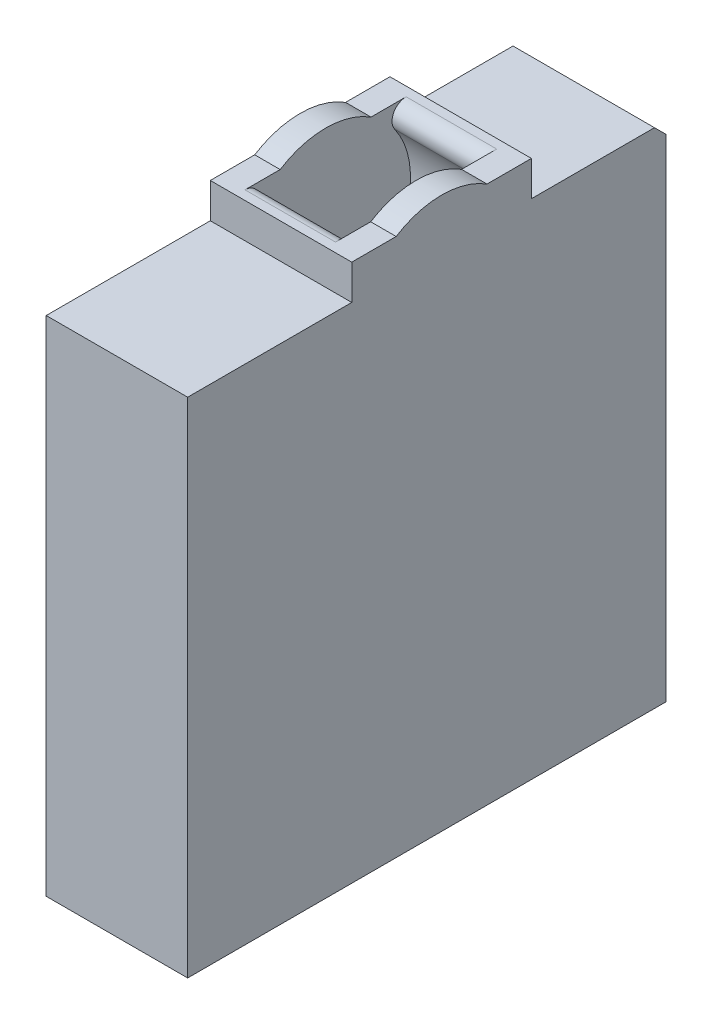
SolidWorks part; units mm, degrees
material "ABS"
ref_plane "Front Plane" through (0, 0, 0) normal (0, 0, 1) x (1, 0, 0)
ref_plane "Top Plane" through (0, 0, 0) normal (0, 1, 0) x (1, 0, 0)
ref_plane "Right Plane" through (0, 0, 0) normal (1, 0, 0) x (0, 0, -1)
sketch "Sketch1" plane through (0, 0, 0) normal (1, 0, 0) x (0, 0, -1)
  line L0 (-44.875, -95.07) -> (-44.875, -6.17)
  line L1 (-44.875, -6.17) -> (-15.875, -6.17)
  line L2 (-15.875, -6.17) -> (-15.875, 0)
  line L3 (-15.875, 0) -> (15.875, 0)
  line L4 (15.875, 0) -> (15.875, -6.17)
  line L5 (15.875, -6.17) -> (39.625, -6.17)
  line L6 (39.625, -6.17) -> (39.625, -95.07)
  line L7 (39.625, -95.07) -> (-44.875, -95.07)
  point P4 (0, 0)
  dimension "D1" = 88.9
  dimension "D2" = 6.17
  dimension "D3" = 29
  dimension "D4" = 23.75
  dimension "D5" = 31.75
extrude "Boss-Extrude1" add sketch "Sketch1" along normal blind 25
sketch "Sketch2" plane through (25, 0, 0) normal (1, 0, 0) x (0, 0, -1)
  line L0 (-15.875, -6.17) -> (15.875, -6.17) construction
  line L1 (0, -6.17) -> (0, 2.33) construction
  line L2 (-8.0294, 0) -> (8.0294, 0)
  line L3 (15.875, 0) -> (-15.875, 0) construction
  arc A0 (8.0294, 0) -> (-8.0294, 0) centre (0, -12.67) ccw
  dimension "D2" = 30
  dimension "D1" = 8.5
extrude "Boss-Extrude2" add sketch "Sketch2" against normal up to surface (25 mm away) up to face at (0, -26.8525, 1.3125)
sketch "Sketch3" plane through (25, 0, 0) normal (1, 0, 0) x (0, 0, -1)
  circle A0 centre (0, -12.67) radius 15
  arc A1 (8.0294, 0) -> (-8.0294, 0) centre (0, -12.67) ccw construction
extrude "Cut-Extrude1" cut sketch "Sketch3" against normal offset from surface (16 mm away) 4.5 from offset 4.5 up to face at (0, -21.249, 1.05) offset against normal yes
sketch "Sketch4" plane through (0, 0, 0) normal (-1, 0, 0) x (0, 0, 1)
  line L0 (-8.0294, 0) -> (-13.081, 9.8406)
  line L1 (-13.081, 9.8406) -> (-10.6667, 11.08)
  line L2 (-10.6667, 11.08) -> (-5.6151, 1.2394)
  line L3 (-11.8739, 10.4603) -> (0, -12.67) construction
  line L4 (-39.625, -6.17) -> (-15.875, -6.17) construction
  circle A0 centre (0, -12.67) radius 15
  arc A1 (8.0294, 0) -> (-8.0294, 0) centre (0, -12.67) ccw construction
  dimension "D1" = 17.25
  dimension "D2" = 26
  dimension "D3" = 2.7139
chamfer "Chamfer1" distance 2 angle 45 1 edges at (12.5, -6.17, -39.625)
fillet "Fillet2" radius 2.5 2 edges at (12.5, 0, -8.0294) (12.5, 0, 8.0294)
